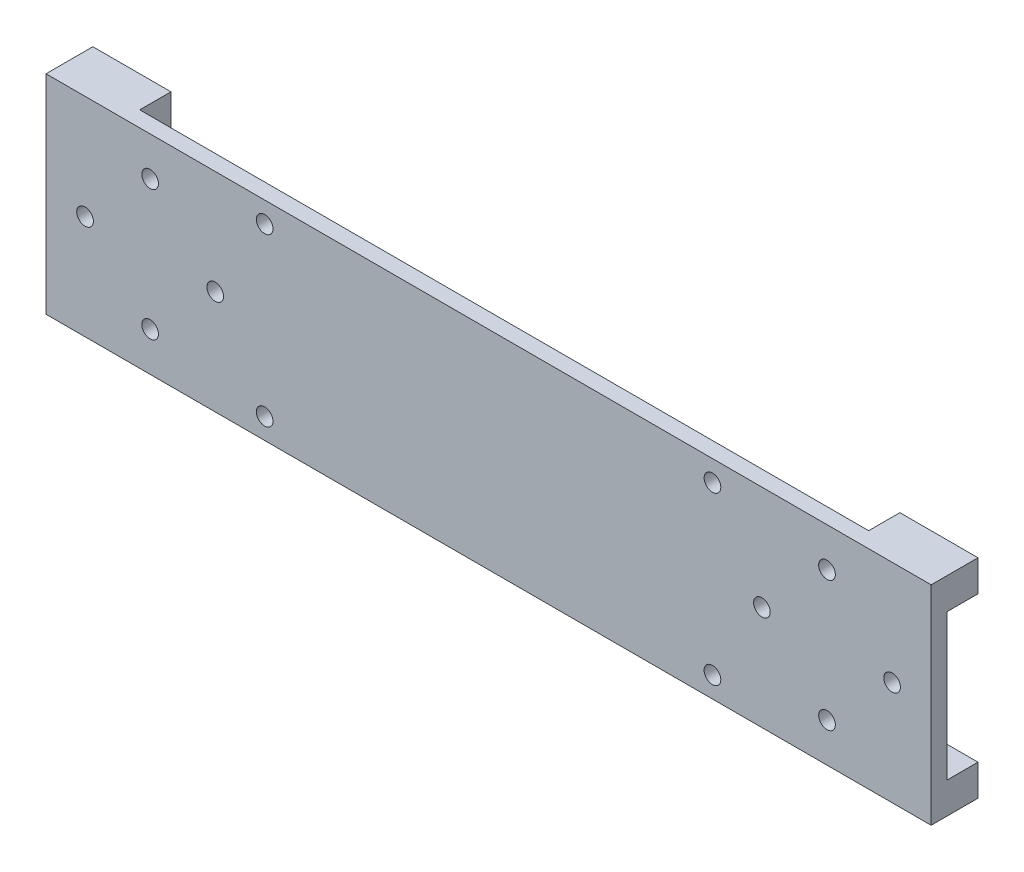
SolidWorks part; units mm, degrees
ref_plane "前视基准面" through (0, 0, 0) normal (0, 0, 1) x (1, 0, 0)
ref_plane "上视基准面" through (0, 0, 0) normal (0, 1, 0) x (1, 0, 0)
ref_plane "右视基准面" through (0, 0, 0) normal (1, 0, 0) x (0, 0, -1)
other "Configuration Table"
sketch "草图1" plane through (0, 0, 0) normal (0, 0, 1) x (1, 0, 0)
  line L0 (-6.504, 16.029) -> (-6.504, -23.971) construction
  line L1 (-91.504, 16.029) -> (78.496, 16.029)
  line L2 (-91.504, 16.029) -> (-91.504, -23.971)
  line L3 (-91.504, -23.971) -> (78.496, -23.971)
  line L4 (78.496, 16.029) -> (78.496, -23.971)
  line L5 (-91.504, -3.971) -> (-6.504, -3.971) construction
  circle A0 centre (-71.504, -3.971) radius 12.5 construction
  circle A1 centre (-71.504, 8.529) radius 1.6
  circle A2 centre (-59.004, -3.971) radius 1.6
  circle A3 centre (-71.504, -16.471) radius 1.6
  circle A4 centre (-84.004, -3.971) radius 1.6
  circle A5 centre (70.996, -3.971) radius 1.6
  circle A6 centre (58.496, 8.529) radius 1.6
  circle A7 centre (58.496, -16.471) radius 1.6
  circle A8 centre (45.996, -3.971) radius 1.6
  dimension "D4" = 25
  dimension "D5" = 3.2
  dimension "D1" = 170
  dimension "D2" = 40
  dimension "D3" = 20
extrude "凸台-拉伸1" add sketch "草图1" along normal blind 3
sketch "草图2" plane through (0, 0, 0) normal (0, 0, -1) x (-1, 0, 0)
  line L0 (6.504, 16.029) -> (6.504, -23.971) construction
  line L1 (-78.496, 16.029) -> (91.504, 16.029) construction
  line L2 (91.504, -23.971) -> (-78.496, -23.971) construction
  line L4 (-36.496, 12.029) -> (49.504, 12.029) construction
  line L5 (-36.496, 12.029) -> (-36.496, -19.971) construction
  line L6 (-36.496, -19.971) -> (49.504, -19.971) construction
  line L7 (49.504, 12.029) -> (49.504, -19.971) construction
  circle A0 centre (-36.496, 12.029) radius 1.6
  circle A1 centre (-36.496, -19.971) radius 1.6
  circle A2 centre (49.504, 12.029) radius 1.6
  circle A3 centre (49.504, -19.971) radius 1.6
  point P10 (6.504, 12.029)
  point P11 (-36.496, -3.971)
  point P12 (6.504, -3.971)
  dimension "D3" = 3.2
  dimension "D1" = 86
  dimension "D2" = 32
extrude "切除-拉伸1" cut sketch "草图2" against normal through all
sketch "草图3" plane through (0, 0, 0) normal (0, 0, -1) x (-1, 0, 0)
  line L0 (-78.496, -3.971) -> (91.504, -3.971) construction
  line L1 (-78.496, 16.029) -> (-63.496, 16.029)
  line L2 (-78.496, 16.029) -> (-78.496, 10.029)
  line L3 (-78.496, 10.029) -> (-63.496, 10.029)
  line L4 (-63.496, 16.029) -> (-63.496, 10.029)
  line L5 (-78.496, -23.971) -> (-78.496, 16.029) construction
  line L6 (91.504, 16.029) -> (91.504, -23.971) construction
  line L7 (6.504, 16.029) -> (6.504, -23.971) construction
  line L8 (-78.496, 16.029) -> (91.504, 16.029) construction
  line L9 (91.504, -23.971) -> (-78.496, -23.971) construction
  line L10 (-78.496, -17.971) -> (-63.496, -17.971)
  line L11 (-63.496, -23.971) -> (-63.496, -17.971)
  line L12 (-78.496, -23.971) -> (-63.496, -23.971)
  line L13 (-78.496, -23.971) -> (-78.496, -17.971)
  line L14 (91.504, 10.029) -> (76.504, 10.029)
  line L15 (76.504, 16.029) -> (76.504, 10.029)
  line L16 (91.504, 16.029) -> (76.504, 16.029)
  line L17 (91.504, 16.029) -> (91.504, 10.029)
  line L18 (91.504, -23.971) -> (91.504, -17.971)
  line L19 (91.504, -23.971) -> (76.504, -23.971)
  line L20 (76.504, -23.971) -> (76.504, -17.971)
  line L21 (91.504, -17.971) -> (76.504, -17.971)
  dimension "D1" = 15
  dimension "D2" = 6
extrude "凸台-拉伸2" add sketch "草图3" along normal blind 6
